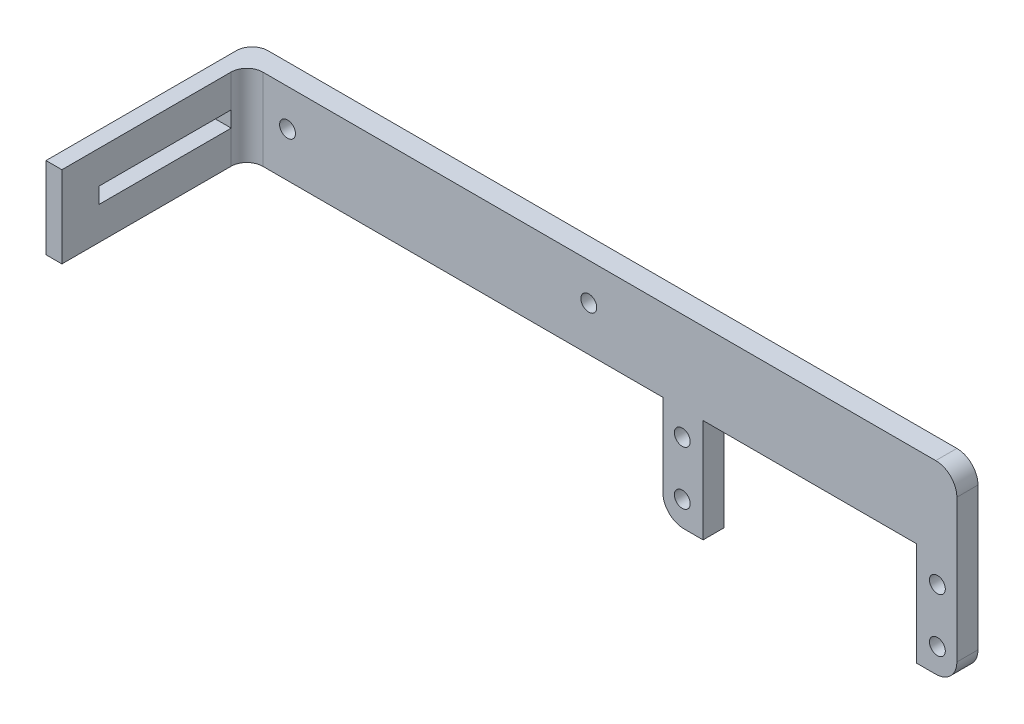
SolidWorks part; units mm, degrees
material "Acrylic (Medium-high impact)"
ref_plane "Front Plane" through (0, 0, 0) normal (0, 0, 1) x (1, 0, 0)
ref_plane "Top Plane" through (0, 0, 0) normal (0, 1, 0) x (1, 0, 0)
ref_plane "Right Plane" through (0, 0, 0) normal (1, 0, 0) x (0, 0, -1)
sketch "Sketch2" plane through (0, 0, 0) normal (0, 0, 1) x (1, 0, 0)
  line L0 (-67.0811, 16.9235) -> (-26.6951, 16.9235)
  line L1 (-26.6951, 16.9235) -> (-26.6951, -2.6345)
  line L2 (-26.6951, -2.6345) -> (-19.0751, -2.6345)
  line L3 (-19.0751, -2.6345) -> (-19.0751, 32.3655)
  line L4 (-19.0751, 32.3655) -> (-67.0811, 32.3655)
  line L6 (-74.7011, 16.9235) -> (-74.7011, -2.6345)
  line L7 (-74.7011, -2.6345) -> (-67.0811, -2.6345)
  line L8 (-67.0811, -2.6345) -> (-67.0811, 16.9235)
  line L9 (-67.0811, 16.9235) -> (-67.1703, 16.7363)
  line L10 (-74.7011, 32.3655) -> (-67.0811, 32.3655)
  line L11 (-159.7011, 16.9235) -> (-74.7011, 16.9235)
  line L12 (-159.3598, 32.8744) -> (-156.3911, 32.8744)
  line L13 (-159.3598, 32.8744) -> (-159.3598, 16.9235)
  line L14 (-159.3598, 16.9235) -> (-156.3911, 16.9235)
  line L15 (-156.3911, 32.8744) -> (-156.3911, 16.9235)
  line L17 (-159.7011, 16.9235) -> (-159.7011, 32.3655)
  line L23 (-159.7011, 32.3655) -> (-74.7011, 32.3655)
  line L24 (-159.7011, 32.3655) -> (-159.3598, 32.8744)
extrude "Boss-Extrude2" add sketch "Sketch2" along normal blind 4
fillet "Fillet1" radius 4 3 edges at (-74.7011, -2.6345, 2) (-19.0751, -2.6345, 2) (-19.0751, 32.3655, 2)
sketch "Sketch3" plane through (0, 0, 4) normal (0, 0, 1) x (1, 0, 0)
  line L4 (-74.7011, 16.9235) -> (-74.7011, 1.3655) construction
  circle A0 centre (-145.7011, 25.3655) radius 1.5
  circle A1 centre (-88.7011, 25.3655) radius 1.5
  dimension "D3" = 14
sketch "Sketch6" plane through (0, 0, 4) normal (0, 0, 1) x (1, 0, 0)
  line L0 (-67.0811, -2.6345) -> (-67.0811, 16.9235) construction
  line L3 (-67.0811, 16.9235) -> (-26.6951, 16.9235) construction
  circle A4 centre (-71.0181, 12.2245) radius 1.5
  circle A5 centre (-22.7581, 12.2245) radius 1.5
  circle A6 centre (-22.7581, 2.0645) radius 1.5
  circle A7 centre (-71.0181, 2.0645) radius 1.5
  dimension "D5" = 3.937
  dimension "D6" = 4.699
  dimension "D7" = 2
  dimension "D8" = 2
extrude "Cut-Extrude1" cut sketch "Sketch6" against normal blind 4
extrude "Cut-Extrude2" cut sketch "Sketch3" against normal blind 4 contours A0 | A1
sketch "Sketch7" plane through (0, 0, 4) normal (0, 0, 1) x (1, 0, 0)
  line L0 (-156.3911, 16.9235) -> (-74.7011, 16.9235) construction
  line L1 (-156.3911, 32.3655) -> (-153.3845, 32.3655)
  line L2 (-156.3911, 32.3655) -> (-156.3911, 16.9235)
  line L3 (-156.3911, 16.9235) -> (-153.3845, 16.9235)
  line L4 (-153.3845, 32.3655) -> (-153.3845, 16.9235)
extrude "Boss-Extrude3" add sketch "Sketch7" along normal blind 35
fillet "Fillet2" radius 3 1 edges at (-153.3845, 24.6445, 4)
fillet "Fillet3" radius 3 1 edges at (-156.3911, 24.6445, 0)
sketch "Sketch8" plane through (-156.3911, 0, 0) normal (-1, 0, 0) x (0, 0, 1)
  line L0 (31.967, 26.1655) -> (31.967, 23.1655)
  line L1 (6.967, 26.1655) -> (31.967, 26.1655)
  line L2 (6.967, 26.1655) -> (6.967, 23.1655)
  line L3 (6.967, 23.1655) -> (31.967, 23.1655)
  line L4 (39, 16.9235) -> (3, 16.9235) construction
  line L5 (39, 32.3655) -> (3, 32.3655) construction
  dimension "D1" = 6.2
extrude "Cut-Extrude6" cut sketch "Sketch8" along normal blind 4 and the other way blind 4
